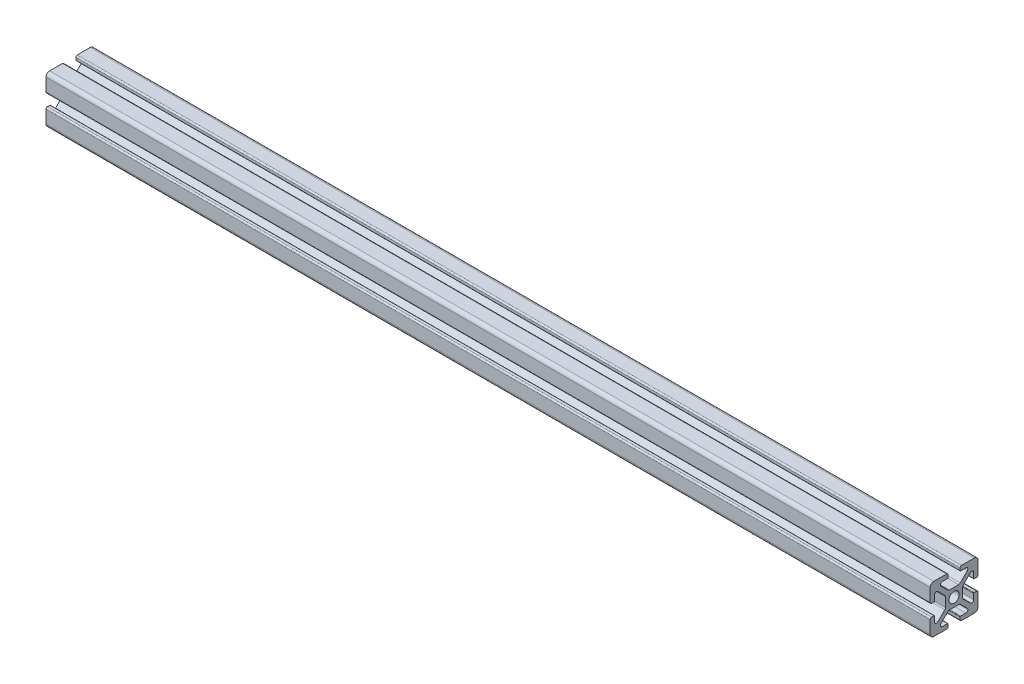
SolidWorks part; units mm, degrees
ref_plane "Front Plane" through (0, 0, 0) normal (0, 0, 1) x (1, 0, 0)
ref_plane "Top Plane" through (0, 0, 0) normal (0, 1, 0) x (1, 0, 0)
ref_plane "Right Plane" through (0, 0, 0) normal (1, 0, 0) x (0, 0, -1)
sketch "Sketch1" plane through (0, 0, 0) normal (1, 0, 0) x (0, 0, -1)
  line L0 (0, -10) -> (0, 10) construction
  line L1 (10, -10) -> (-10, -10)
  line L2 (10, -10) -> (10, 10)
  line L3 (10, 10) -> (0, 10)
  line L4 (-10, -10) -> (-10, 10)
  line L5 (10, -10) -> (-10, 10) construction
  line L6 (10, 10) -> (-10, -10) construction
  line L7 (10, 0) -> (-10, 0) construction
  line L8 (-2.5, 9.4) -> (-2.5, 8.3731)
  line L9 (-2.7, 8.1731) -> (-4.95, 8.1731)
  line L10 (-5.5157, 6.8075) -> (-2.6011, 3.8929)
  line L11 (-1.894, 3.6) -> (0, 3.6)
  line L12 (-5.3502, 4.0584) -> (-4.0584, 5.3502) construction
  line L13 (-3.825, 8.1731) -> (-3.825, 10) construction
  line L14 (-3.1, 10) -> (-10, 10)
  line L15 (-5.75, 7.3731) -> (5.75, 7.3731) construction
  circle A0 centre (0, 0) radius 2.15
  arc A1 (-4.95, 8.1731) -> (-5.5157, 6.8075) centre (-4.95, 7.3731) ccw
  arc A2 (-2.6011, 3.8929) -> (-1.894, 3.6) centre (-1.894, 4.6) ccw
  arc A3 (-2.5, 8.3731) -> (-2.7, 8.1731) centre (-2.7, 8.3731) cw
  arc A4 (-2.5, 9.4) -> (-3.1, 10) centre (-3.1, 9.4) ccw
  point P0 (0, 0)
  point P9 (0, 0)
  point P12 (0, 0)
  point P22 (-4.7043, 4.7043)
  point P32 (-2.5, 10)
  point P33 (-2.5, 8.8866)
  point P35 (-4.0584, 5.3502)
  point P37 (0, 7.3731)
  point P38 (-3.825, 10)
  point P39 (-3.825, 8.1731)
  point P40 (-3.825, 10)
  point P41 (-2.7, 8.1731)
  point P42 (-2.7, 8.1731)
  dimension "Center Hole Diameter" = 4.3
  dimension "D4" = 1
  dimension "D5" = 0.2
  dimension "D6" = 0.6
  dimension "D3" = 0.8
  dimension "Rail Height" = 20
  dimension "D7" = 6.4
  dimension "T Slot Width" = 5
  dimension "D10" = 10
  dimension "Rail Width" = 20
  dimension "D2" = 11.5
  dimension "D8" = 1.0269
sketch "Sketch2" plane through (0, 0, 0) normal (0, 0, 1) x (1, 0, 0)
  line L0 (-132.4, 10) -> (-132.4, -10) construction
  line L1 (152.4, -10) -> (-152.4, -10) construction
  line L2 (152.4, -10) -> (152.4, 10) construction
  line L3 (152.4, 10) -> (-152.4, 10) construction
  line L4 (-152.4, -10) -> (-152.4, 10) construction
  line L5 (152.4, -10) -> (-152.4, 10) construction
  line L6 (152.4, 10) -> (-152.4, -10) construction
  line L7 (132.4, 10) -> (132.4, -10) construction
  point P0 (0, 0)
  point P12 (132.4, 0)
  dimension "Length" = 304.8
  dimension "D1" = 20
  dimension "D2" = 20
sketch "Sketch3" plane through (0, 0, 0) normal (1, 0, 0) x (0, 0, -1)
  line L0 (-5.5157, 6.8075) -> (-2.6011, 3.8929) construction
  line L5 (-3.1, 10) -> (-10, 10) construction
  line L6 (-2.5, 9.4) -> (-2.5, 8.3731) construction
  line L7 (-2.7, 8.1731) -> (-4.95, 8.1731) construction
  line L8 (-1.894, 3.6) -> (0, 3.6) construction
  line L9 (-5.5157, 6.8075) -> (-2.6011, 3.8929)
  line L10 (-10, 10) -> (0, 0) construction
  line L12 (-3.6, 1.894) -> (-3.6, 0)
  line L13 (-8.1731, 2.7) -> (-8.1731, 4.95)
  line L14 (-3.1, 10) -> (-8.5, 10)
  line L15 (-2.5, 9.4) -> (-2.5, 8.3731)
  line L16 (-2.7, 8.1731) -> (-4.95, 8.1731)
  line L17 (-1.894, 3.6) -> (0, 3.6)
  line L18 (-9.4, 2.5) -> (-8.3731, 2.5)
  line L19 (-10, 3.1) -> (-10, 8.5)
  line L20 (-6.8075, 5.5157) -> (-3.8929, 2.6011)
  line L21 (-3.6, 0) -> (-2.15, 0)
  line L22 (0, 3.6) -> (0, 2.15)
  arc A0 (-2.5, 9.4) -> (-3.1, 10) centre (-3.1, 9.4) ccw construction
  arc A1 (-2.7, 8.1731) -> (-2.5, 8.3731) centre (-2.7, 8.3731) ccw construction
  arc A2 (-4.95, 8.1731) -> (-5.5157, 6.8075) centre (-4.95, 7.3731) ccw construction
  arc A3 (-2.6011, 3.8929) -> (-1.894, 3.6) centre (-1.894, 4.6) ccw construction
  arc A4 (-2.5, 9.4) -> (-3.1, 10) centre (-3.1, 9.4) ccw
  arc A5 (-2.7, 8.1731) -> (-2.5, 8.3731) centre (-2.7, 8.3731) ccw
  arc A6 (-4.95, 8.1731) -> (-5.5157, 6.8075) centre (-4.95, 7.3731) ccw
  arc A7 (-2.6011, 3.8929) -> (-1.894, 3.6) centre (-1.894, 4.6) ccw
  arc A8 (-3.8929, 2.6011) -> (-3.6, 1.894) centre (-4.6, 1.894) cw
  arc A9 (-8.1731, 4.95) -> (-6.8075, 5.5157) centre (-7.3731, 4.95) cw
  arc A10 (-8.1731, 2.7) -> (-8.3731, 2.5) centre (-8.3731, 2.7) cw
  arc A11 (-9.4, 2.5) -> (-10, 3.1) centre (-9.4, 3.1) cw
  circle A12 centre (0, 0) radius 2.15 construction
  arc A13 (0, 2.15) -> (-2.15, 0) centre (0, 0) ccw
  arc A14 (-10, 8.5) -> (-8.5, 10) centre (-8.5, 8.5) cw
  dimension "D1" = 1.5
extrude "Boss-Extrude1" add sketch "Sketch3" against normal blind 370
mirror "Mirror1" about plane through (0, 0, 0) normal (0, 1, 0) of bodies 104
mirror "Mirror2" about plane through (0, 0, 0) normal (0, 0, 1) of bodies 105
equation "\"D10@Sketch1\" = \"Rail Height@Sketch1\" / 2"
equation "\"D2@Sketch2\"=\"D1@Sketch2\""
